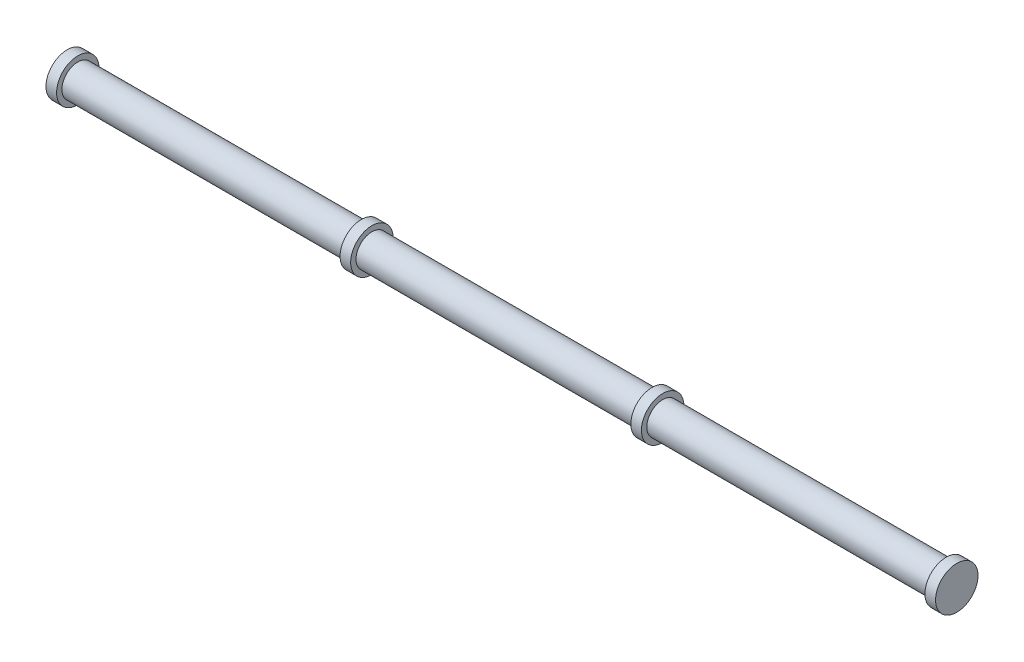
SolidWorks part; units mm, degrees
ref_plane "Front Plane" through (0, 0, 0) normal (0, 0, 1) x (1, 0, 0)
ref_plane "Top Plane" through (0, 0, 0) normal (0, 1, 0) x (1, 0, 0)
ref_plane "Right Plane" through (0, 0, 0) normal (1, 0, 0) x (0, 0, -1)
sketch "Sketch1" plane through (0, 0, 0) normal (1, 0, 0) x (0, 0, -1)
  circle A0 centre (0, 0) radius 7.5
  dimension "D1" = 15
extrude "Boss-Extrude1" add sketch "Sketch1" along normal mid plane 408.94
sketch "Sketch2" plane through (204.47, 0, 0) normal (1, 0, 0) x (0, 0, -1)
  circle A0 centre (0, 0) radius 10
  dimension "D1" = 20
extrude "Boss-Extrude2" add sketch "Sketch2" along normal blind 5 separate body
mirror "Mirror1" about plane through (0, 0, 0) normal (1, 0, 0) of bodies 102
combine bodies "Combine1" operation type add bodies to combine 103 102 101
ref_plane "Plane1" through (-68.47, 0, 0) normal (1, 0, 0) x (0, 0, -1)
ref_plane "Plane2" through (68.47, 0, 0) normal (-1, 0, 0) x (0, 0, 1)
sketch "Sketch3" plane through (-68.47, 0, 0) normal (1, 0, 0) x (0, 0, -1)
  circle A1 centre (0, 0) radius 10
  circle A2 centre (0, 0) radius 10
  dimension "D1" = 0
extrude "Boss-Extrude3" add sketch "Sketch3" along normal mid plane 5
sketch "Sketch4" plane through (68.47, 0, 0) normal (-1, 0, 0) x (0, 0, 1)
  circle A1 centre (0, 0) radius 10
  circle A2 centre (0, 0) radius 10
  dimension "D1" = 0
extrude "Boss-Extrude4" add sketch "Sketch4" along normal mid plane 5
